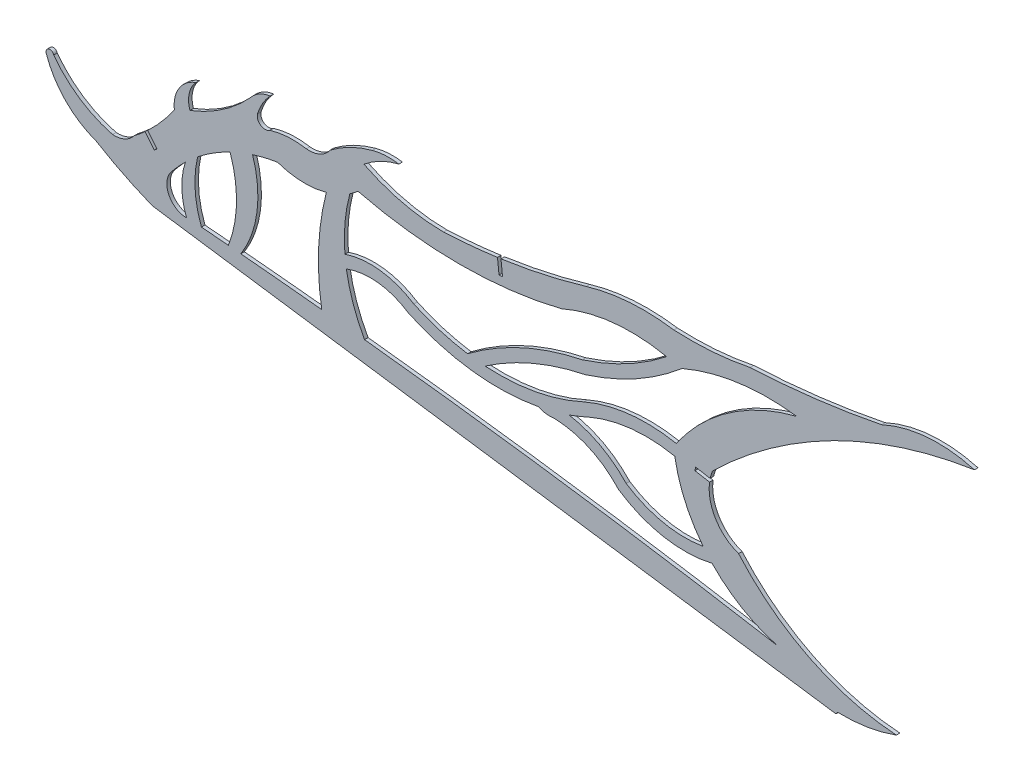
SolidWorks part; units mm, degrees
ref_plane "Front Plane" through (0, 0, 0) normal (0, 0, 1) x (1, 0, 0)
ref_plane "Top Plane" through (0, 0, 0) normal (0, 1, 0) x (1, 0, 0)
ref_plane "Right Plane" through (0, 0, 0) normal (1, 0, 0) x (0, 0, -1)
sketch "Sketch1" plane through (0, 0, 0) normal (0, 0, 1) x (1, 0, 0)
  line L1 (299.4967, 247.0839) -> (293.2284, 248.1915)
  line L2 (59.2104, 228.6183) -> (353.7115, 186.322)
  line L3 (299.2315, 245.5832) -> (292.9633, 246.6907)
  line L5 (293.2284, 248.1915) -> (292.9633, 246.6907)
  line L7 (56.0303, 254.7624) -> (60.0092, 249.8666)
  line L8 (57.1563, 255.7933) -> (61.1919, 250.8278)
  line L10 (60.0092, 249.8666) -> (61.1919, 250.8278)
  line L16 (207.8646, 283.7423) -> (208.537, 277.4529)
  line L17 (209.3745, 283.9557) -> (210.0523, 277.6149)
  line L19 (208.537, 277.4529) -> (210.0523, 277.6149)
  arc A0 (328.4892, 199.1824) -> (150.587, 224.4222) centre (-162.1365, -2619.3982) ccw
  arc A1 (73.8894, 231.5214) -> (67.2104, 245.2524) centre (73.8894, 240.0113) cw
  arc A2 (67.2104, 245.2524) -> (73.3905, 252.0345) centre (124.5978, 199.1655) cw
  arc A3 (113.1016, 271.8646) -> (134.1291, 271.1114) centre (124.818, 305.0644) ccw
  arc A4 (147.764, 278.3627) -> (235.3903, 278.3404) centre (191.6224, 455.7178) ccw
  arc A5 (235.3903, 278.3404) -> (280.7309, 283.139) centre (265.4708, 210.7226) cw
  arc A6 (287.3938, 282.0436) -> (336.809, 288.8939) centre (324.523, 195.8646) cw
  arc A7 (336.809, 288.8939) -> (284.9063, 252.8219) centre (358.7017, 202.0169) ccw
  arc A8 (328.4892, 199.1824) -> (300.3136, 215.8121) centre (344.1075, 257.8283) cw
  arc A9 (144.2693, 275.7191) -> (142.123, 252.0465) centre (210.2297, 257.8053) ccw
  arc A10 (134.1291, 271.1114) -> (132.143, 226.3899) centre (238.9874, 244.0497) ccw
  arc A11 (92.6374, 265.4667) -> (91.9104, 230.2633) centre (44.56, 248.8504) cw
  arc A12 (102.3578, 269.3275) -> (97.2848, 229.779) centre (58.0743, 254.9083) cw
  arc A13 (78.6655, 256.6768) -> (80.3107, 231.2736) centre (120.5235, 246.6327) ccw
  arc A14 (73.3905, 252.0345) -> (73.8894, 231.5214) centre (102.254, 242.4738) ccw
  arc A15 (78.6655, 256.6768) -> (92.6374, 265.4667) centre (124.5978, 199.1655) cw
  arc A16 (102.3578, 269.3275) -> (113.1016, 271.8646) centre (124.5978, 199.1655) cw
  arc A17 (91.9104, 230.2633) -> (80.3107, 231.2736) centre (-162.1365, -2619.3982) ccw
  arc A18 (132.143, 226.3899) -> (97.2848, 229.779) centre (-162.1365, -2619.3982) ccw
  arc A19 (144.2693, 275.7191) -> (147.764, 278.3627) centre (124.818, 305.0644) ccw
  arc A20 (283.8697, 250.4336) -> (246.0954, 246.1006) centre (272.037, 186.7681) ccw construction
  arc A21 (246.0954, 246.1006) -> (170.5568, 246.1006) centre (208.3261, 327.781) cw construction
  arc A22 (142.7591, 246.8782) -> (150.587, 224.4222) centre (210.2297, 257.8053) ccw
  arc A23 (284.9063, 252.8219) -> (245.0531, 248.417) centre (272.037, 186.7681) ccw
  arc A24 (245.0531, 248.417) -> (202.5166, 240.5241) centre (208.3261, 327.781) cw
  arc A25 (171.7898, 248.3291) -> (142.123, 252.0465) centre (153.121, 219.5791) ccw
  arc A26 (284.2565, 247.7721) -> (247.1369, 243.7838) centre (272.037, 186.7681) ccw
  arc A27 (247.1369, 243.7838) -> (238.6943, 240.3763) centre (208.3261, 327.781) cw
  arc A28 (169.3146, 243.8768) -> (142.7591, 246.8782) centre (153.121, 219.5791) ccw
  arc A29 (57.1563, 255.7933) -> (68.6319, 269.199) centre (3.2114, 313.5861) ccw
  arc A30 (299.2315, 245.5832) -> (311.7555, 225.1575) centre (318.0025, 243.0402) ccw
  arc A31 (209.3745, 283.9557) -> (246.0954, 292.0212) centre (172.4306, 539.7815) ccw
  arc A58 (34.9897, 240.6666) -> (59.2104, 228.6183) centre (118.3133, 377.8025) ccw
  arc A59 (353.7115, 186.322) -> (354.4333, 187.2865) centre (319.8251, 212.434) ccw
  arc A60 (354.4333, 187.2865) -> (379.7362, 191.4119) centre (356.4501, 254.5755) ccw
  arc A61 (311.7555, 225.1575) -> (379.7362, 191.4119) centre (386.3361, 290.0542) ccw
  arc A62 (300.5625, 250.4336) -> (299.4967, 247.0839) centre (318.0025, 243.0402) ccw
  arc A63 (343.5995, 282.8928) -> (300.5625, 250.4336) centre (448.6234, 98.8832) ccw
  arc A64 (413.3877, 307.235) -> (343.5995, 282.8928) centre (444.2474, 106.5502) ccw
  arc A65 (413.3877, 307.235) -> (373.3389, 304.0502) centre (397.6657, 251.5406) ccw
  arc A66 (316.7305, 297.0926) -> (373.3389, 304.0502) centre (298.5777, 678.5526) ccw
  arc A67 (283.8697, 294.6521) -> (316.7305, 297.0926) centre (290.7187, 424.8879) ccw
  arc A68 (283.8697, 294.6521) -> (246.0954, 292.0212) centre (270.8801, 208.6617) ccw
  arc A69 (184.6162, 281.5894) -> (207.8646, 283.7423) centre (172.4306, 539.7815) ccw
  arc A70 (150.3405, 289.7385) -> (184.6162, 281.5894) centre (184.7892, 358.4744) ccw
  arc A71 (165.4063, 297.3313) -> (150.3405, 289.7385) centre (174.096, 261.3457) ccw
  arc A72 (165.4063, 297.3313) -> (153.9595, 296.712) centre (161.1352, 270.1793) ccw
  arc A73 (153.9595, 296.712) -> (135.7697, 287.7262) centre (167.6472, 246.1006) ccw
  arc A74 (125.5196, 283.0817) -> (135.7697, 287.7262) centre (126.7443, 294.0116) ccw
  arc A75 (125.5196, 283.0817) -> (109.7471, 282.1054) centre (119.6632, 249.7989) ccw
  arc A76 (104.4417, 285.5283) -> (109.7471, 282.1054) centre (107.7252, 284.7946) ccw
  arc A77 (109.9211, 294.9774) -> (104.4417, 285.5283) centre (127.7241, 278.3404) ccw
  arc A78 (109.9211, 294.9774) -> (101.5754, 290.3041) centre (111.5891, 282.21) ccw
  arc A79 (75.3557, 272.3016) -> (101.5754, 290.3041) centre (50.6742, 336.3439) ccw
  arc A80 (77.9793, 284.0254) -> (75.3557, 272.3016) centre (86.3085, 276.0059) ccw
  arc A81 (77.9793, 284.0254) -> (68.6319, 269.199) centre (82.4264, 270.8619) ccw
  arc A82 (51.3192, 250.8509) -> (56.0303, 254.7624) centre (3.2114, 313.5861) ccw
  arc A83 (42.0381, 246.6774) -> (51.3192, 250.8509) centre (42.7992, 257.3914) ccw
  arc A84 (16.6466, 263.6546) -> (42.0381, 246.6774) centre (53.2769, 290.963) ccw
  arc A85 (16.6466, 263.6546) -> (13.4695, 262.5682) centre (15.0185, 263.2273) ccw
  arc A86 (13.4695, 262.5682) -> (34.9897, 240.6666) centre (47.067, 274.057) ccw
  arc A87 (198.6043, 240.873) -> (245.0531, 261.3457) centre (269.4821, 142.9925) cw construction
  arc A88 (245.0531, 261.3457) -> (283.8697, 282.4058) centre (209.5546, 373.0765) ccw construction
  arc A89 (232.4415, 238.4487) -> (261.6885, 225.1575) centre (231.2923, 197.0956) cw construction
  arc A90 (261.6885, 225.1575) -> (298.3341, 217.9778) centre (288.6273, 265.544) ccw construction
  arc A91 (232.3709, 235.9097) -> (260.0207, 223.2179) centre (231.2923, 197.0956) cw
  arc A92 (260.0207, 223.2179) -> (300.3136, 215.8121) centre (288.6273, 265.544) ccw
  arc A93 (202.5166, 240.5241) -> (245.6947, 258.8845) centre (269.4821, 142.9925) cw
  arc A94 (245.6947, 258.8845) -> (287.3938, 282.0436) centre (209.5546, 373.0765) ccw
  arc A95 (238.6943, 240.3763) -> (263.343, 227.1082) centre (231.2923, 197.0956) cw
  arc A96 (263.343, 227.1082) -> (296.4805, 220.2127) centre (288.6273, 265.544) ccw
  arc A97 (194.9867, 241.3543) -> (244.4087, 263.8061) centre (269.4821, 142.9925) cw
  arc A98 (244.4087, 263.8061) -> (280.7309, 283.139) centre (209.5546, 373.0765) ccw
  arc A106 (296.4805, 220.2127) -> (284.2565, 247.7721) centre (344.1075, 257.8283) cw
  arc A108 (232.3709, 235.9097) -> (225.3958, 236.8391) centre (230.4109, 247.8385) cw
  arc A110 (225.3958, 236.8391) -> (169.3146, 243.8768) centre (208.3261, 327.781) cw
  arc A111 (194.9867, 241.3543) -> (171.7898, 248.3291) centre (208.3261, 327.781) cw
  point P98 (300.6823, 246.1006)
  point P99 (293.0959, 247.4411)
  point P101 (300.8149, 246.851)
  point P106 (141.534, 251.8409)
  point P113 (300.5497, 245.3502)
  point P129 (200.0941, 238.8158)
  point P132 (55.1685, 257.0309)
  point P134 (232.512, 240.9877)
  point P137 (297.8262, 220.4665)
  point P139 (60.6006, 250.3472)
  point P142 (282.2596, 284.3703)
  point P156 (54.5772, 256.5503)
  point P158 (55.7599, 257.5115)
  point P166 (208.3261, 286.5943)
  point P167 (209.2946, 277.5339)
  point P168 (207.5684, 286.5133)
  point P170 (209.0838, 286.6753)
extrude "Boss-Extrude1" add sketch "Sketch1" along normal blind 1.524
